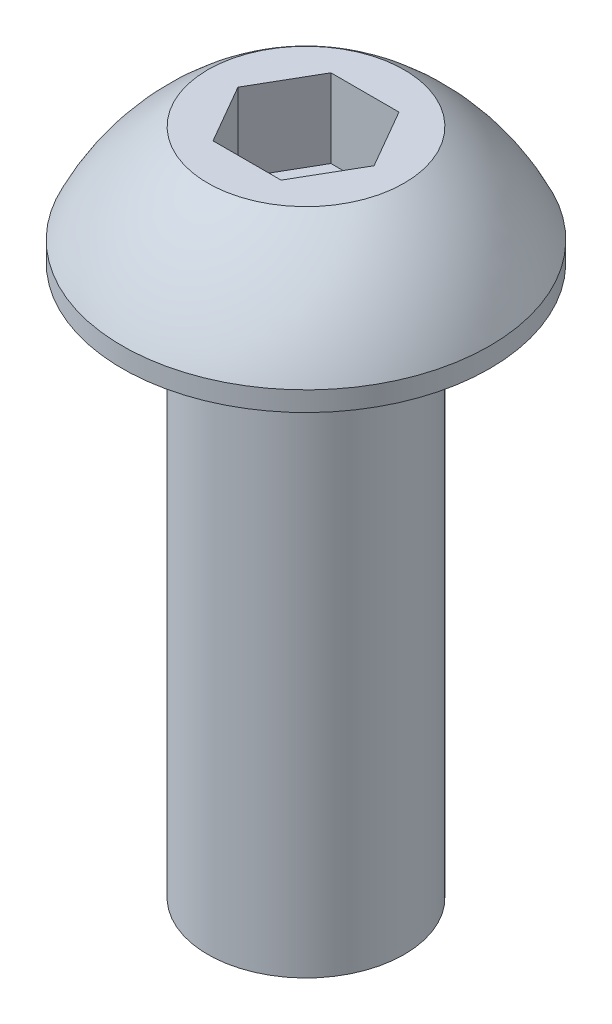
SolidWorks part; units mm, degrees
material "AISI 304"
ref_plane "Front Plane" through (0, 0, 0) normal (0, 0, 1) x (1, 0, 0)
ref_plane "Top Plane" through (0, 0, 0) normal (0, 1, 0) x (1, 0, 0)
ref_plane "Right Plane" through (0, 0, 0) normal (1, 0, 0) x (0, 0, -1)
sketch "Sketch1" plane through (0, 0, 0) normal (0, 0, 1) x (1, 0, 0)
  line L0 (2.5, 0) -> (4.675, 0)
  line L1 (4.675, 0) -> (4.675, 0.5)
  line L2 (2.5, 3) -> (0, 3)
  line L3 (2.5, 0) -> (2.5, -14)
  line L4 (2.5, -14) -> (0, -14)
  line L5 (0, -14) -> (0, 3)
  arc A0 (4.675, 0.5) -> (2.5, 3) centre (-0.7631, -2.0351) ccw
  dimension "D5" = 6
  dimension "D1" = 2.5
  dimension "D2" = 14
  dimension "D3" = 4.675
  dimension "D4" = 3
  dimension "D6" = 0.5
  dimension "D7" = 2.5
revolve "Revolve1" add sketch "Sketch1" angle 360 about L5
sketch "Sketch2" plane through (0, 3, 0) normal (0, 1, 0) x (1, 0, 0)
  line L1 (0.866, 1.5) -> (-0.866, 1.5)
  line L2 (-0.866, 1.5) -> (-1.7321, 0)
  line L3 (-1.7321, 0) -> (-0.866, -1.5)
  line L4 (-0.866, -1.5) -> (0.866, -1.5)
  line L5 (0.866, -1.5) -> (1.7321, 0)
  line L6 (1.7321, 0) -> (0.866, 1.5)
  circle A0 centre (0, 0) radius 1.5 construction
  dimension "D1" = 3
extrude "Cut-Extrude1" cut sketch "Sketch2" against normal blind 2
